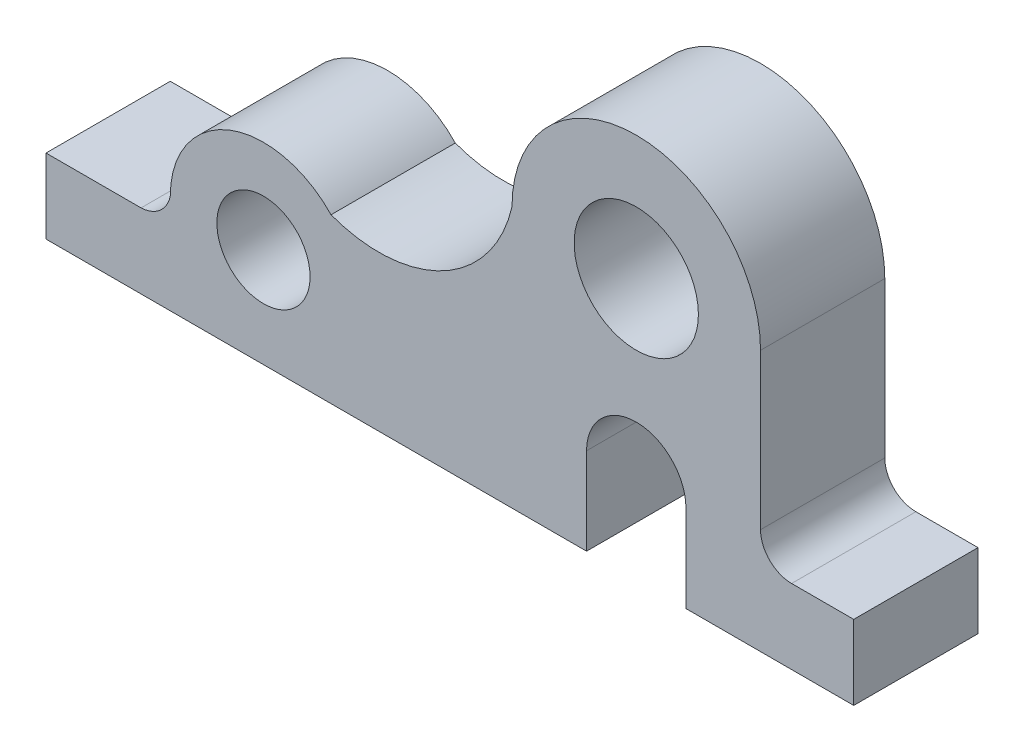
SolidWorks part; units mm, degrees
ref_plane "Front Plane" through (0, 0, 0) normal (0, 0, 1) x (1, 0, 0)
ref_plane "Top Plane" through (0, 0, 0) normal (0, 1, 0) x (1, 0, 0)
ref_plane "Right Plane" through (0, 0, 0) normal (1, 0, 0) x (0, 0, -1)
sketch "Sketch1" plane through (0, 0, 0) normal (0, 0, 1) x (1, 0, 0)
  line L0 (0, 0) -> (87, 0)
  line L1 (87, 0) -> (87, 14)
  line L2 (115, 42) -> (115, 17)
  line L3 (103, 14) -> (103, 0)
  line L4 (103, 0) -> (130, 0)
  line L5 (130, 0) -> (130, 12)
  line L6 (120, 12) -> (130, 12)
  line L7 (0, 0) -> (0, 12)
  line L8 (0, 12) -> (15.3, 12)
  circle A0 centre (35, 16) radius 7.5
  arc A1 (45.8746, 26.3316) -> (20, 16) centre (35, 16) ccw
  arc A2 (15.3, 12) -> (20, 16) centre (15.1002, 16.996) ccw
  arc A3 (87, 14) -> (103, 14) centre (95, 14) cw
  circle A4 centre (95, 42) radius 10
  arc A5 (115, 42) -> (75, 42) centre (95, 42) ccw
  arc A6 (115, 17) -> (120, 12) centre (120, 17) ccw
  arc A7 (45.8746, 26.3316) -> (75, 42) centre (53.5628, 46.9445) ccw
  dimension "D8" = 15
  dimension "D9" = 30
  dimension "D10" = 5
  dimension "D11" = 8
  dimension "D12" = 20
  dimension "D13" = 40
  dimension "D14" = 35
  dimension "D16" = 5
  dimension "D18" = 22
  dimension "D1" = 12
  dimension "D2" = 14
  dimension "D3" = 130
  dimension "D4" = 16
  dimension "D5" = 15.3
  dimension "D6" = 16
  dimension "D7" = 35
  dimension "D15" = 28
  dimension "D17" = 12
extrude "Boss-Extrude1" add sketch "Sketch1" along normal mid plane 20
